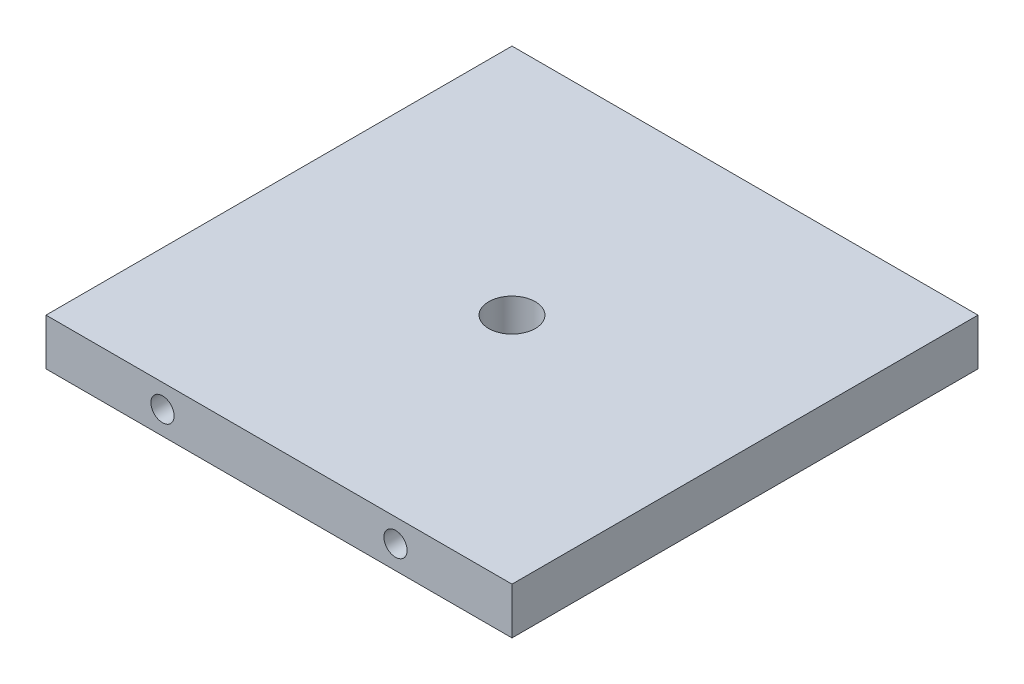
SolidWorks part; units mm, degrees
ref_plane "Спереди" through (0, 0, 0) normal (0, 0, 1) x (1, 0, 0)
ref_plane "Сверху" through (0, 0, 0) normal (0, 1, 0) x (1, 0, 0)
ref_plane "Справа" through (0, 0, 0) normal (1, 0, 0) x (0, 0, -1)
sketch "Эскиз1" plane through (0, 0, 0) normal (0, 1, 0) x (1, 0, 0)
  line L1 (-50, -50) -> (50, -50)
  line L2 (-50, -50) -> (-50, 50)
  line L3 (-50, 50) -> (50, 50)
  line L4 (50, -50) -> (50, 50)
  line L5 (-50, -50) -> (50, 50) construction
  line L6 (-50, 50) -> (50, -50) construction
  point P0 (0, 0)
  dimension "D1" = 100
extrude "Бобышка-Вытянуть1" add sketch "Эскиз1" along normal blind 10
sketch "Эскиз2" plane through (0, 0, 50) normal (0, 0, 1) x (1, 0, 0)
  line L0 (-50, 20.5427) -> (0, 20.5427) construction
  line L1 (0, 20.5427) -> (50, 20.5427) construction
  circle A0 centre (-25, 5) radius 2.5
  circle A1 centre (25, 5) radius 2.5
  dimension "D3" = 5
  dimension "D4" = 5
  dimension "D1" = 50
  dimension "D2" = 50
extrude "Вырез-Вытянуть1" cut sketch "Эскиз2" against normal blind 10
sketch "Эскиз3" plane through (0, 0, -50) normal (0, 0, -1) x (-1, 0, 0)
  line L0 (-50, 17.3073) -> (0, 17.3073) construction
  line L1 (0, 17.3073) -> (50, 17.3073) construction
  circle A0 centre (-25, 5) radius 2.5
  circle A1 centre (25, 5) radius 2.5
  dimension "D3" = 5
  dimension "D4" = 5
  dimension "D1" = 50
  dimension "D2" = 50
extrude "Вырез-Вытянуть2" cut sketch "Эскиз3" against normal blind 10
sketch "Эскиз4" plane through (0, 10, 0) normal (0, 1, 0) x (1, 0, 0)
  circle A0 centre (0, 0) radius 5
  dimension "D1" = 10
extrude "Вырез-Вытянуть3" cut sketch "Эскиз4" against normal through all
